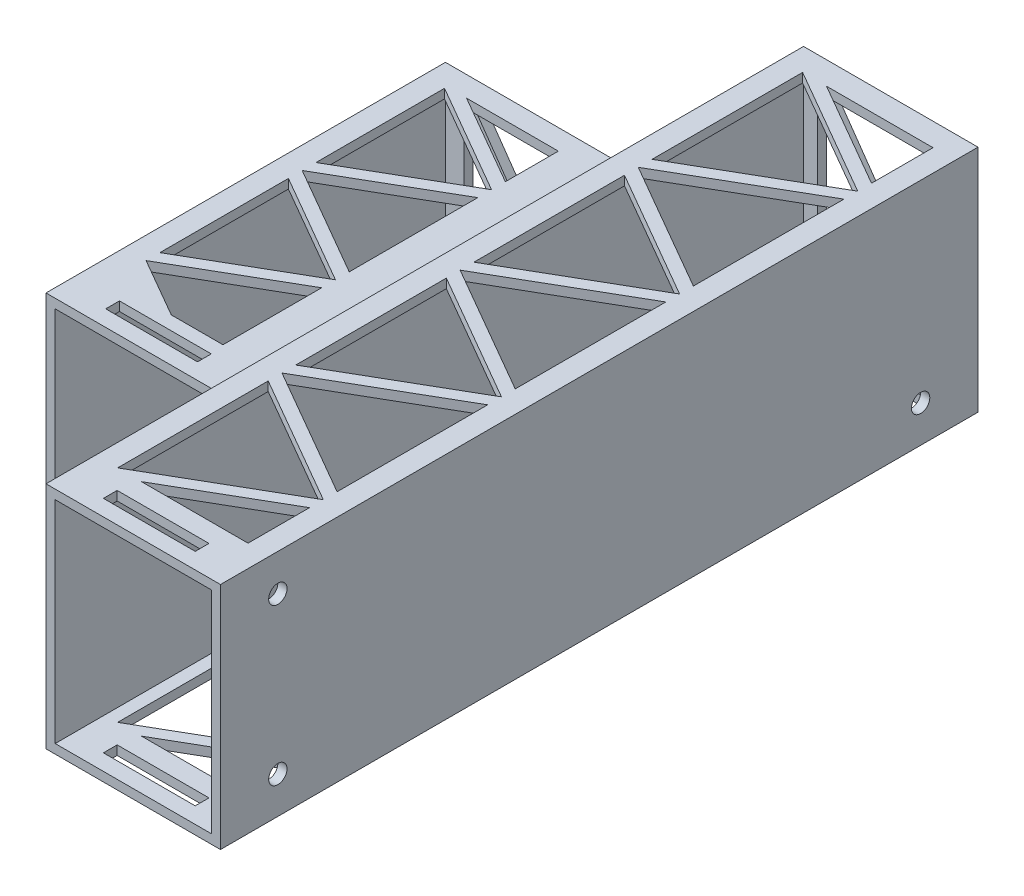
SolidWorks part; units mm, degrees
ref_plane "Front Plane" through (0, 0, 0) normal (0, 0, 1) x (1, 0, 0)
ref_plane "Top Plane" through (0, 0, 0) normal (0, 1, 0) x (1, 0, 0)
ref_plane "Right Plane" through (0, 0, 0) normal (1, 0, 0) x (0, 0, -1)
sketch "BodySketch" plane through (0, 0, 0) normal (1, 0, 0) x (0, 0, -1)
  line L1 (-82.5, -25) -> (82.5, -25)
  line L2 (-82.5, -25) -> (-82.5, 25)
  line L3 (-82.5, 25) -> (82.5, 25)
  line L4 (82.5, -25) -> (82.5, 25)
  line L5 (-82.5, -25) -> (82.5, 25) construction
  line L6 (-82.5, 25) -> (82.5, -25) construction
  point P0 (0, 0)
  dimension "D1" = 50
  dimension "D2" = 165
extrude "Body" add sketch "BodySketch" along normal blind 38
sketch "HoleSketch" plane through (0, 0, 82.5) normal (0, 0, 1) x (1, 0, 0)
  line L0 (0.3836, 0) -> (0, 0)
  line L1 (0, 0) -> (32.8071, 0) construction
  line L2 (19, 22.5) -> (19, 0.724) construction
  line L4 (38, 25) -> (0, 25) construction
  line L5 (36, 23) -> (2, 23)
  line L6 (36, 23) -> (36, -23)
  line L7 (36, -23) -> (2, -23)
  line L8 (2, 23) -> (2, -23)
  line L9 (36, 23) -> (2, -23) construction
  line L10 (36, -23) -> (2, 23) construction
  line L11 (38, 25) -> (38, -25) construction
  line L12 (0, 25) -> (0, -25) construction
  point P6 (19, 0)
  dimension "D1" = 2
  dimension "D2" = 2
  dimension "D3" = 2
  dimension "D4" = 46
  dimension "D5" = 34
extrude "Hole" cut sketch "HoleSketch" against normal blind 163 contours L5 L8 L7 L6
sketch "SecondBatterySketch" plane through (0, 0, 0) normal (-1, 0, 0) x (0, 0, 1)
  line L0 (0, 0) -> (45.2856, 0) construction
  line L1 (0, 0) -> (0, 36.9572) construction
  line L3 (43.5, -22) -> (-43.5, -22)
  line L4 (43.5, -22) -> (43.5, 22)
  line L5 (43.5, 22) -> (-43.5, 22)
  line L6 (-43.5, -22) -> (-43.5, 22)
  line L7 (43.5, -22) -> (-43.5, 22) construction
  line L8 (43.5, 22) -> (-43.5, -22) construction
  point P4 (0, 0)
  dimension "D1" = 44
  dimension "D2" = 87
extrude "SecondBattery" add sketch "SecondBatterySketch" along normal blind 39
sketch "SecondBatteryHoleSketch" plane through (0, 0, 43.5) normal (0, 0, 1) x (1, 0, 0)
  line L1 (-17.8443, 0) -> (-1.5339, 0) construction
  line L2 (-18.5, 22) -> (-18.5, -22) construction
  line L6 (0, 20) -> (-37, 20)
  line L7 (0, 20) -> (0, -20)
  line L8 (0, -20) -> (-37, -20)
  line L9 (-37, 20) -> (-37, -20)
  line L10 (0, 20) -> (-37, -20) construction
  line L11 (0, -20) -> (-37, 20) construction
  line L13 (-39, -22) -> (-39, 22) construction
  point P3 (-18.5, 0)
  dimension "D1" = 40
  dimension "D2" = 37
  dimension "D3" = 2
extrude "SecondBatteryHole" cut sketch "SecondBatteryHoleSketch" against normal blind 85
sketch "ConnectorSketch" plane through (38, 0, 0) normal (1, 0, 0) x (0, 0, -1)
  line L0 (0, 17) -> (0, -17) construction
  line L1 (70, -17) -> (-70, -17) construction
  line L2 (0, 17) -> (-70, 17) construction
  circle A0 centre (-70, 17) radius 2
  circle A1 centre (-70, -17) radius 2
  circle A2 centre (70, -17) radius 2
  point P4 (0, 0)
  point P9 (0, -17)
  dimension "D3" = 4
  dimension "D1" = 34
  dimension "D2" = 140
extrude "Cut-Extrude3" cut sketch "ConnectorSketch" against normal blind 15
sketch "StrapSketch" plane through (0, 25, 0) normal (0, 1, 0) x (1, 0, 0)
  line L0 (38, -82.5) -> (0, -82.5) construction
  line L1 (19, -82.5) -> (19, -77.5) construction
  line L2 (-19.5, -43.5) -> (-19.5, -38.5) construction
  line L3 (29, -76) -> (9, -76)
  line L4 (29, -76) -> (29, -79)
  line L5 (29, -79) -> (9, -79)
  line L6 (9, -76) -> (9, -79)
  line L7 (29, -76) -> (9, -79) construction
  line L8 (29, -79) -> (9, -76) construction
  line L9 (-39, -43.5) -> (0, -43.5) construction
  line L11 (-9.5, -37) -> (-29.5, -37)
  line L12 (-9.5, -37) -> (-9.5, -40)
  line L13 (-9.5, -40) -> (-29.5, -40)
  line L14 (-29.5, -37) -> (-29.5, -40)
  line L15 (-9.5, -37) -> (-29.5, -40) construction
  line L16 (-9.5, -40) -> (-29.5, -37) construction
  dimension "D1" = 5
  dimension "D2" = 3
  dimension "D3" = 20
  dimension "D4" = 5
  dimension "D5" = 20
  dimension "D6" = 3
extrude "Cut-Extrude4" cut sketch "StrapSketch" against normal through all
sketch "WeightReduction" plane through (0, 25, 0) normal (0, 1, 0) x (1, 0, 0)
  line L0 (4.8, 77.5) -> (4.8, 44.7)
  line L1 (4.8, 44.7) -> (33.2056, 61.1)
  line L2 (33.2056, 61.1) -> (4.8, 77.5)
  line L3 (0, 82.5) -> (0, -82.5) construction
  line L4 (38, 82.5) -> (0, 82.5) construction
  line L5 (33.2056, -19.5) -> (33.2056, -52.3)
  line L6 (33.2056, -52.3) -> (4.8, -35.9)
  line L7 (33.2056, 58.1) -> (33.2056, 25.3)
  line L8 (33.2056, 25.3) -> (4.8, 41.7)
  line L9 (4.8, 41.7) -> (33.2056, 58.1)
  line L10 (4.8, 38.7) -> (4.8, 5.9)
  line L11 (4.8, 5.9) -> (33.2056, 22.3)
  line L12 (33.2056, 22.3) -> (4.8, 38.7)
  line L13 (33.2056, 19.3) -> (33.2056, -13.5)
  line L14 (33.2056, -13.5) -> (4.8, 2.9)
  line L15 (4.8, 2.9) -> (33.2056, 19.3)
  line L16 (4.8, -0.1) -> (4.8, -32.9)
  line L17 (4.8, -32.9) -> (33.2056, -16.5)
  line L18 (33.2056, -16.5) -> (4.8, -0.1)
  line L19 (4.8, -35.9) -> (33.2056, -19.5)
  line L20 (4.8, -38.9) -> (4.8, -71.7)
  line L21 (4.8, -71.7) -> (33.2056, -55.3)
  line L22 (33.2056, -55.3) -> (4.8, -38.9)
  line L23 (33.2056, -58.3) -> (33.2056, -71.7)
  line L24 (33.2056, -71.7) -> (9.9962, -71.7)
  line L25 (9.9962, -71.7) -> (33.2056, -58.3)
  line L26 (33.2056, 64.1) -> (33.2056, 77.5)
  line L27 (33.2056, 77.5) -> (9.9962, 77.5)
  line L28 (9.9962, 77.5) -> (33.2056, 64.1)
  line L29 (-34.2, 38.5) -> (-34.2, 10.5)
  line L30 (-34.2, 10.5) -> (-9.9513, 24.5)
  line L31 (-9.9513, 24.5) -> (-34.2, 38.5)
  line L32 (-39, 43.5) -> (0, 43.5) construction
  line L35 (-39, -43.5) -> (-39, 43.5) construction
  line L36 (-9.9513, 21.5) -> (-9.9513, -6.5)
  line L37 (-9.9513, -6.5) -> (-34.2, 7.5)
  line L38 (-34.2, 7.5) -> (-9.9513, 21.5)
  line L39 (-34.2, 4.5) -> (-34.2, -23.5)
  line L40 (-34.2, -23.5) -> (-9.9513, -9.5)
  line L41 (-9.9513, -9.5) -> (-34.2, 4.5)
  line L42 (-34.2, -26.5) -> (-9.9513, -12.5)
  line L47 (-9.9513, 27.5) -> (-9.9513, 39.047)
  line L48 (-9.9513, 39.047) -> (-29.9513, 39.047)
  line L49 (-29.9513, 39.047) -> (-9.9513, 27.5)
  line L50 (-9.9513, -12.5) -> (-9.9513, -34)
  line L51 (-9.9513, -34) -> (-21.2096, -34)
  line L52 (-21.2096, -34) -> (-34.2, -26.5)
  line L53 (-29.5, -37) -> (-9.5, -37) construction
  dimension "D1" = 60
  dimension "D2" = 4.8
  dimension "D3" = 5
  dimension "D4" = 60
  dimension "D5" = 3
  dimension "D6" = 60
  dimension "D7" = 60
  dimension "D8" = 32.8
  dimension "D9" = 32.8
  dimension "D10" = 3
  dimension "D11" = 60
  dimension "D12" = 60
  dimension "D13" = 32.8
  dimension "D14" = 3
  dimension "D15" = 32.8
  dimension "D16" = 60
  dimension "D17" = 60
  dimension "D18" = 3
  dimension "D19" = 32.8
  dimension "D20" = 60
  dimension "D21" = 60
  dimension "D22" = 3
  dimension "D23" = 32.8
  dimension "D24" = 60
  dimension "D25" = 60
  dimension "D26" = 60
  dimension "D27" = 60
  dimension "D28" = 3
  dimension "D29" = 32.8
  dimension "D30" = 3
  dimension "D31" = 3
  dimension "D32" = 5
  dimension "D33" = 60
  dimension "D34" = 60
  dimension "D35" = 28
  dimension "D36" = 4.8
  dimension "D37" = 9.9513
  dimension "D38" = 3
  dimension "D39" = 28
  dimension "D40" = 60
  dimension "D41" = 60
  dimension "D42" = 3
  dimension "D43" = 28
  dimension "D44" = 60
  dimension "D45" = 60
  dimension "D46" = 3
  dimension "D47" = 3
  dimension "D48" = 60
  dimension "D49" = 3
  dimension "D50" = 3
  dimension "D51" = 60
  dimension "D52" = 21.5
  dimension "D53" = 20
extrude "Cut-Extrude5" cut sketch "WeightReduction" against normal through all
sketch "weightCut" plane through (0, 0, -82.5) normal (0, 0, -1) x (-1, 0, 0)
  line L0 (-33, -20) -> (-33, 20) construction
  line L1 (-33, 20) -> (-5, 20) construction
  line L2 (-5, 20) -> (-5, -20) construction
  line L3 (-5, -20) -> (-33, -20) construction
  line L4 (-38, -25) -> (0, -25) construction
  line L5 (-38, -25) -> (-38, 25) construction
  line L6 (-38, 25) -> (0, 25) construction
  line L7 (0, 22) -> (0, -22) construction
  line L8 (-31, -20) -> (-19, -2.8622)
  line L9 (-19, -2.8622) -> (-7, -20)
  line L10 (-33, -18) -> (-20.3963, 0)
  line L11 (-20.3963, 0) -> (-33, 18)
  line L12 (-31, 20) -> (-19, 2.8622)
  line L13 (-19, 2.8622) -> (-7, 20)
  line L14 (-5, 18) -> (-17.6037, 0)
  line L15 (-17.6037, 0) -> (-5, -18)
  line L24 (39, -22) -> (0, -22) construction
  line L25 (6, -19) -> (33, -19) construction
  line L26 (6, -19) -> (6, 19) construction
  line L27 (6, 19) -> (33, 19) construction
  line L28 (33, -19) -> (33, 19) construction
  line L31 (39, 22) -> (39, -22) construction
  line L32 (39, 22) -> (0, 22) construction
  line L33 (0, -25) -> (0, 25) construction
  line L34 (8, -19) -> (19.5, -2.5763)
  line L35 (19.5, -2.5763) -> (31, -19)
  line L36 (6, -17) -> (17.9035, 0)
  line L37 (17.9035, 0) -> (6, 17)
  line L38 (33, -17) -> (21.0965, 0)
  line L39 (21.0965, 0) -> (33, 17)
  line L40 (8, 19) -> (19.5, 2.5763)
  line L41 (19.5, 2.5763) -> (31, 19)
  line L50 (8, -19) -> (31, -19)
  line L51 (33, -17) -> (33, 17)
  line L52 (31, 19) -> (8, 19)
  line L53 (6, 17) -> (6, -17)
  line L54 (-7, -20) -> (-31, -20)
  line L55 (-33, -18) -> (-33, 18)
  line L56 (-31, 20) -> (-7, 20)
  line L57 (-5, 18) -> (-5, -18)
  point P23 (19.5, 0)
  dimension "D1" = 5
  dimension "D2" = 5
  dimension "D3" = 5
  dimension "D4" = 5
  dimension "D5" = 2
  dimension "D6" = 2
  dimension "D7" = 2
  dimension "D8" = 2
  dimension "D9" = 2
  dimension "D10" = 2
  dimension "D11" = 2
  dimension "D12" = 2
  dimension "D13" = 35
  dimension "D14" = 35
  dimension "D15" = 3
  dimension "D16" = 6
  dimension "D17" = 3
  dimension "D18" = 6
  dimension "D19" = 2
  dimension "D20" = 2
  dimension "D21" = 2
  dimension "D22" = 2
  dimension "D23" = 2
  dimension "D24" = 2
  dimension "D25" = 2
  dimension "D26" = 2
  dimension "D27" = 35
  dimension "D28" = 35
extrude "Cut-Extrude6" cut sketch "weightCut" against normal through all
